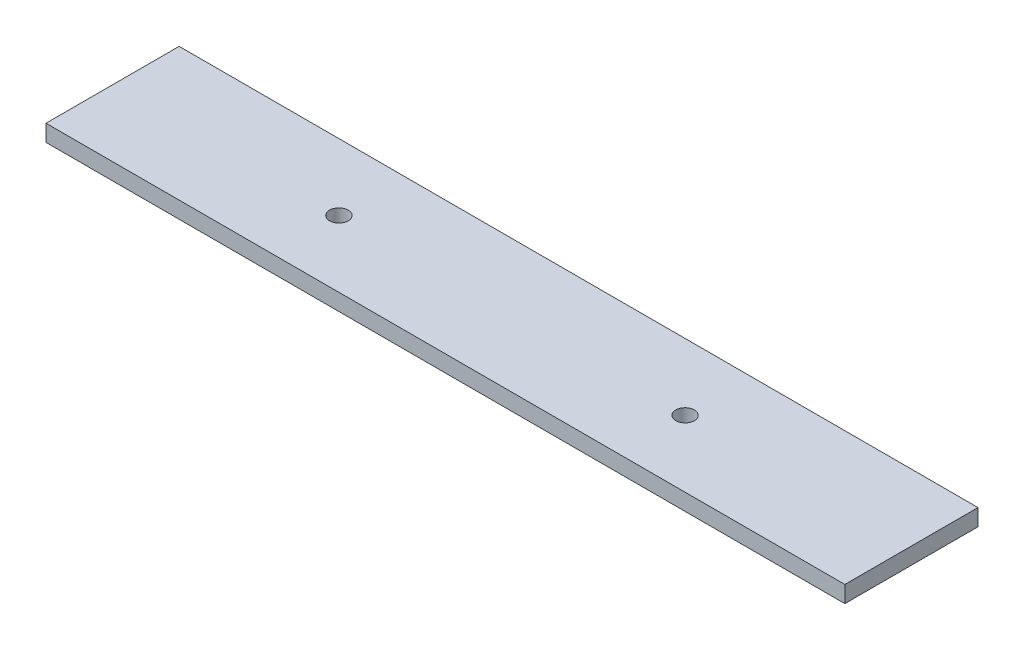
SolidWorks part; units mm, degrees
ref_plane "Front Plane" through (0, 0, 0) normal (0, 0, 1) x (1, 0, 0)
ref_plane "Top Plane" through (0, 0, 0) normal (0, 1, 0) x (1, 0, 0)
ref_plane "Right Plane" through (0, 0, 0) normal (1, 0, 0) x (0, 0, -1)
sketch "Sketch1" plane through (0, 0, 0) normal (0, 1, 0) x (1, 0, 0)
  line L0 (0, 0) -> (66.04, 0) construction
  line L1 (0, 0) -> (-66.04, 0) construction
  line L2 (-152.4, 0) -> (-152.4, 25.4) construction
  line L3 (0, 0) -> (-152.4, 0) construction
  line L5 (152.4, -25.4) -> (-152.4, -25.4)
  line L6 (152.4, -25.4) -> (152.4, 25.4)
  line L7 (152.4, 25.4) -> (-152.4, 25.4)
  line L8 (-152.4, -25.4) -> (-152.4, 25.4)
  line L9 (152.4, -25.4) -> (-152.4, 25.4) construction
  line L10 (152.4, 25.4) -> (-152.4, -25.4) construction
  circle A0 centre (-66.04, 0) radius 3.556
  circle A1 centre (66.04, 0) radius 3.556
extrude "Boss-Extrude1" add sketch "Sketch1" along normal blind 6.35
